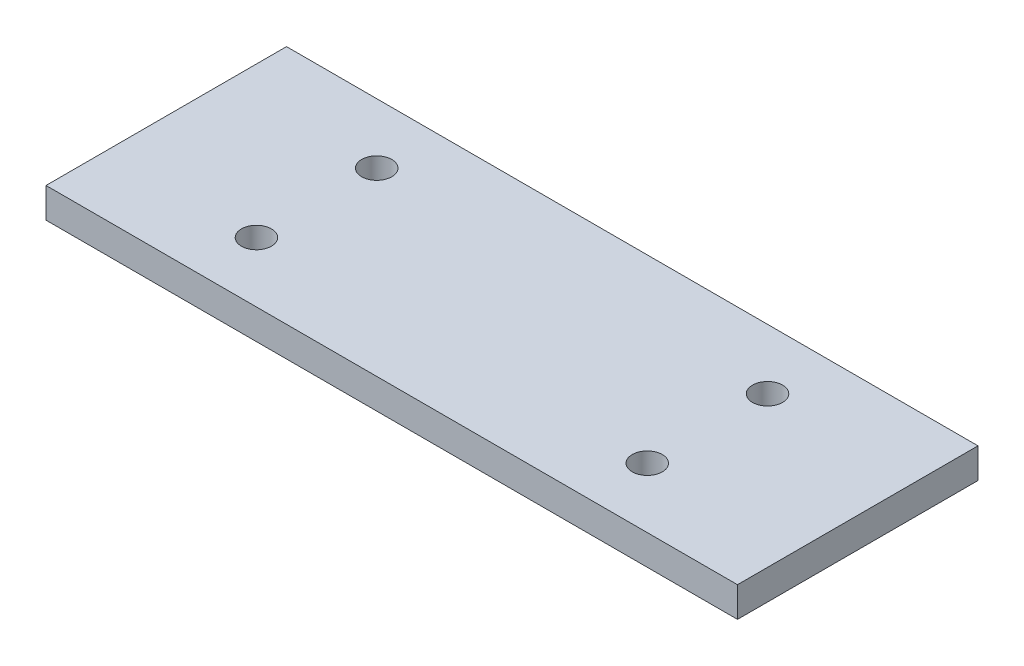
SolidWorks part; units mm, degrees
ref_plane "Front Plane" through (0, 0, 0) normal (0, 0, 1) x (1, 0, 0)
ref_plane "Top Plane" through (0, 0, 0) normal (0, 1, 0) x (1, 0, 0)
ref_plane "Right Plane" through (0, 0, 0) normal (1, 0, 0) x (0, 0, -1)
sketch "Sketch2" plane through (0, 0, 0) normal (0, 1, 0) x (1, 0, 0)
  line L1 (-57.5, -20) -> (57.5, -20)
  line L2 (-57.5, -20) -> (-57.5, 20)
  line L3 (-57.5, 20) -> (57.5, 20)
  line L4 (57.5, -20) -> (57.5, 20)
  circle A0 centre (-32.5, 10) radius 2.5
  circle A1 centre (32.5, 10) radius 2.5
  circle A2 centre (32.5, -10) radius 2.5
  circle A3 centre (-32.5, -10) radius 2.5
  point P0 (0, 0)
  dimension "D5" = 2
  dimension "D7" = 5
  dimension "D1" = 115
  dimension "D2" = 40
  dimension "D3" = 25
  dimension "D4" = 10
  dimension "D6" = 2
extrude "Boss-Extrude1" add sketch "Sketch2" along normal mid plane 5
